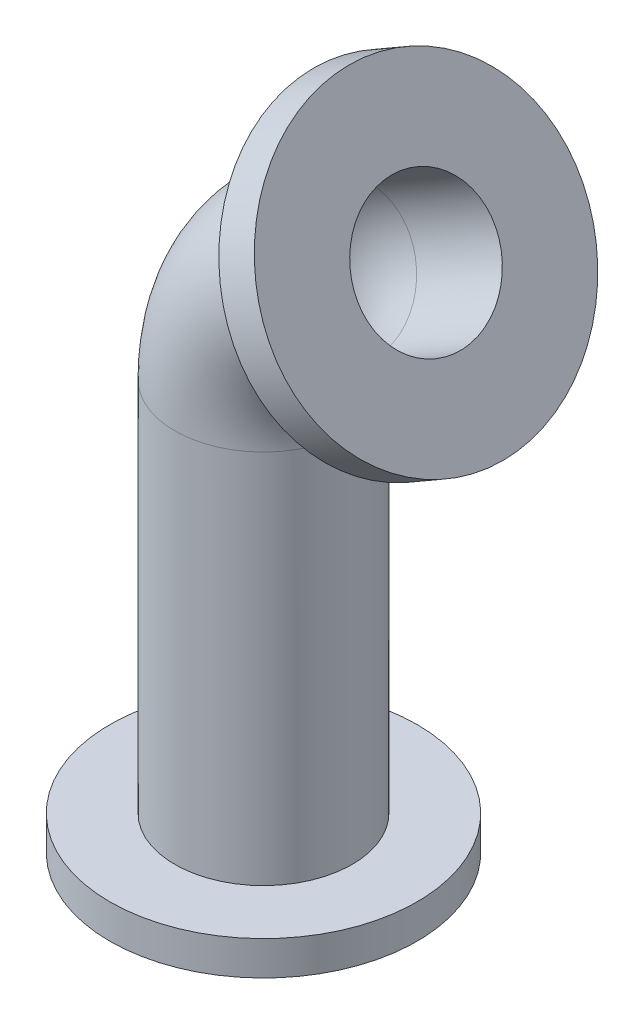
SolidWorks part; units mm, degrees
ref_plane "Vorne" through (0, 0, 0) normal (0, 0, 1) x (1, 0, 0)
ref_plane "Oben" through (0, 0, 0) normal (0, 1, 0) x (1, 0, 0)
ref_plane "Rechts" through (0, 0, 0) normal (1, 0, 0) x (0, 0, -1)
sketch "Skizze1" plane through (0, 0, 0) normal (0, 0, 1) x (1, 0, 0)
  line L0 (0, 0) -> (0, 120)
  line L1 (22.5, 158.9711) -> (47.6147, 173.4711)
  arc A0 (0, 120) -> (22.5, 158.9711) centre (45, 120) cw
  point P6 (0, 146.6688)
  dimension "D3" = 45
  dimension "D1" = 120
  dimension "D2" = 29
  dimension "D4" = 120
sketch "Skizze2" plane through (0, 0, 0) normal (0, 1, 0) x (1, 0, 0)
  circle A0 centre (0, 0) radius 26
  circle A1 centre (0, 0) radius 20
  dimension "D1" = 40
  dimension "D2" = 52
sweep "Austragung1" add profiles "Skizze2" path "Skizze1"
sketch "Skizze3" plane through (0, 0, 0) normal (0, -1, 0) x (1, 0, 0)
  circle A0 centre (0, 0) radius 45
  circle A1 centre (0, 0) radius 26 construction
  circle A2 centre (0, 0) radius 26
  dimension "D1" = 90
extrude "Aufsatz-Linear austragen1" add sketch "Skizze3" against normal blind 10
sketch "Skizze4" plane through (110.8263, 63.9856, 0) normal (0.866, 0.5, 0) x (0, 0, -1)
  circle A0 centre (0, 126.423) radius 45
  circle A1 centre (0, 126.423) radius 26 construction
  circle A2 centre (0, 126.423) radius 26
  dimension "D1" = 90
extrude "Aufsatz-Linear austragen2" add sketch "Skizze4" against normal blind 12
